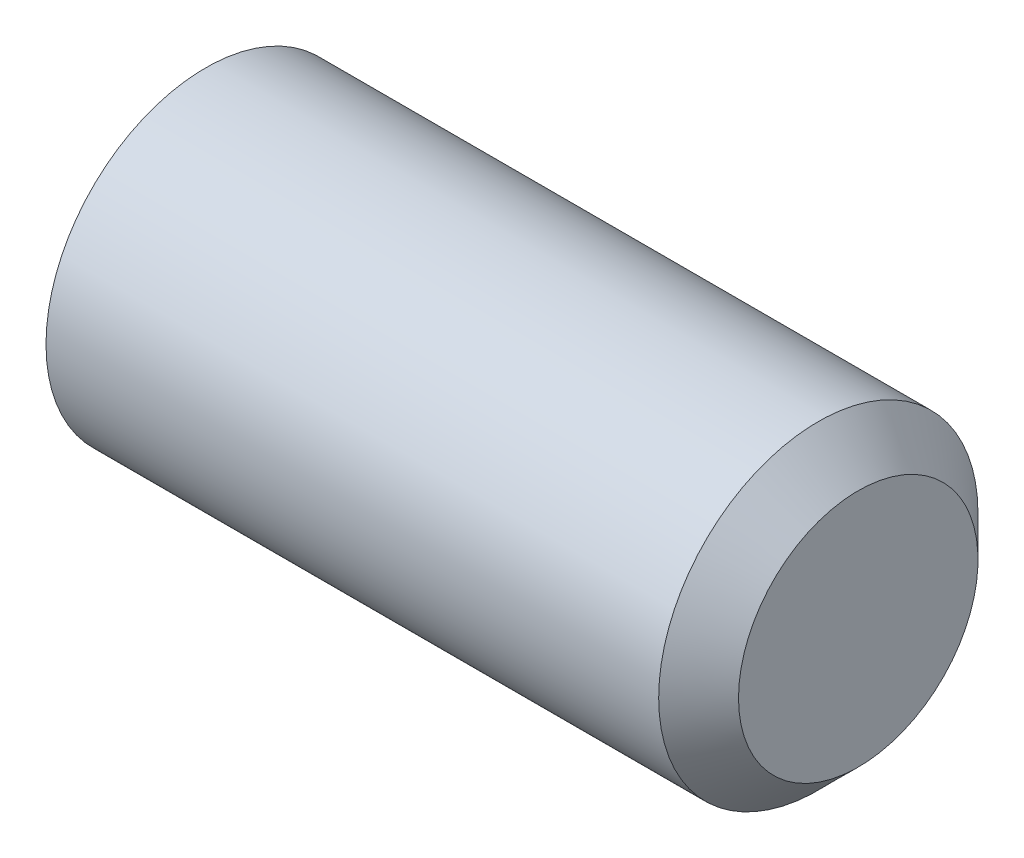
SolidWorks part; units mm, degrees
ref_plane "Plane1" through (0, 0, 0) normal (0, 0, 1) x (1, 0, 0)
ref_plane "Plane2" through (0, 0, 0) normal (0, 1, 0) x (1, 0, 0)
ref_plane "Plane3" through (0, 0, 0) normal (1, 0, 0) x (0, 0, -1)
sketch "BodySke" plane through (0, 0, 0) normal (0, 0, 1) x (1, 0, 0)
  line L0 (0, 0) -> (0, 10.352)
  line L1 (0, 10.352) -> (0.9515, 12)
  line L2 (0.9515, 12) -> (47, 12)
  line L3 (47, 12) -> (50, 9)
  line L4 (50, 0) -> (0, 0)
  line L5 (-12.7, 0) -> (88.9, 0) construction
  line L6 (50, 9) -> (50, 0)
  line L7 (50, 9) -> (50, 18.525) construction
  line L8 (0, -10.352) -> (0.9515, -12) construction
  line L9 (3, 15.875) -> (3, -3.175) construction
  line L10 (47, -12) -> (50, -9) construction
  dimension "Length" = 50
  dimension "Diameter" = 24
  dimension "Drive_ch_ang" = 60
  dimension "Minor_dia" = 20.704
  dimension "Cup_nose_ang" = 45
  dimension "Cup_dia" = 18
  dimension "Advance" = 3
revolve "BaseBody" add sketch "BodySke" angle 360 about L5
cosmetic thread "ThreadCosmetic" parameters "Thread_minor"=20.704
sketch "Sketch2" plane through (0, 0, 0) normal (-1, 0, 0) x (0, 0, 1)
  line L0 (3.4641, 6) -> (-3.4641, 6)
  line L1 (-3.4641, 6) -> (-6.9282, 0)
  line L2 (3.4641, 6) -> (6.9282, 0)
  line L3 (3.4641, -6) -> (6.9282, 0)
  line L4 (3.4641, -6) -> (-3.4641, -6)
  line L5 (-3.4641, -6) -> (-6.9282, 0)
  dimension "Hex_size" = 12
  dimension "D2" = 6
  dimension "D3" = 6
extrude "Hex" cut sketch "Sketch2" against normal blind 15
sketch "ThdSchSke" plane through (0, 0, 0) normal (0, 0, 1) x (1, 0, 0)
  line L0 (0.9515, -10.352) -> (-0.2025, -12)
  line L1 (0.9515, -10.352) -> (2.1054, -12)
  line L2 (2.1054, -12) -> (2.1054, -15)
  line L3 (-3.175, 0) -> (5.1513, 0) construction
  line L5 (2.1054, -15) -> (-0.2025, -15)
  line L6 (-0.2025, -15) -> (-0.2025, -12)
  line L8 (0.9515, 12) -> (0.9515, -12) construction
  dimension "Thread_minor" = 20.704
  dimension "Diameter" = 24
  dimension "SideAngle" = 55
  dimension "VeeAngle" = 70
  dimension "Overcut" = 30
revolve "ThreadSchematic" [suppressed] cut sketch "ThdSchSke" angle 360 about L3
pattern_linear "ThdSchPat" [suppressed]
equation "\"D2@Sketch2\" = \"Hex_size@Sketch2\" / 2"
equation "\"D3@Sketch2\" = \"Hex_size@Sketch2\" / 2"
equation "\"Thread_minor@ThreadCosmetic\" = \"Minor_dia@BodySke\""
equation "\"Thread_minor@ThdSchSke\" = \"Thread_minor@ThreadCosmetic\""
equation "\"Diameter@ThdSchSke\" = \"Diameter@BodySke\""
equation "\"Overcut@ThdSchSke\" = \"Diameter@BodySke\" * 1.25"
equation "\"Num_threads@ThdSchPat\" = int( (\"Length@BodySke\" - ( ( ( \"Diameter@BodySke\" - \"Minor_dia@BodySke\" ) * 0.5 ) / tan( \"Drive_ch_ang@BodySke\" * 0.017453292 ) ) - ( ( ( \"Diameter@BodySke\" - \"Cup_dia@BodySke\" ) * 0.5 ) * tan( \"Cup_nose_ang@BodySke\" * 0.017453292 ) ) ) / \"Advance@BodySke\" + 0.999 )  + 1"
equation "\"Advance@ThdSchPat\" = (\"Length@BodySke\" - ( ( ( \"Diameter@BodySke\" - \"Minor_dia@BodySke\" ) * 0.5 ) / tan( \"Drive_ch_ang@BodySke\" * 0.017453292 ) ) - ( ( ( \"Diameter@BodySke\" - \"Cup_dia@BodySke\" ) * 0.5 ) * tan( \"Cup_nose_ang@BodySke\" * 0.017453292 ) ) ) /  (\"Num_threads@ThdSchPat\" - 1) 'relax it"
equation "' \"Num_threads@ThdSchPat\" = \"Num_threads@ThdSchPat\" - sgn( \"Num_threads@ThdSchPat\" - 1) '---chamfered tips only---"
